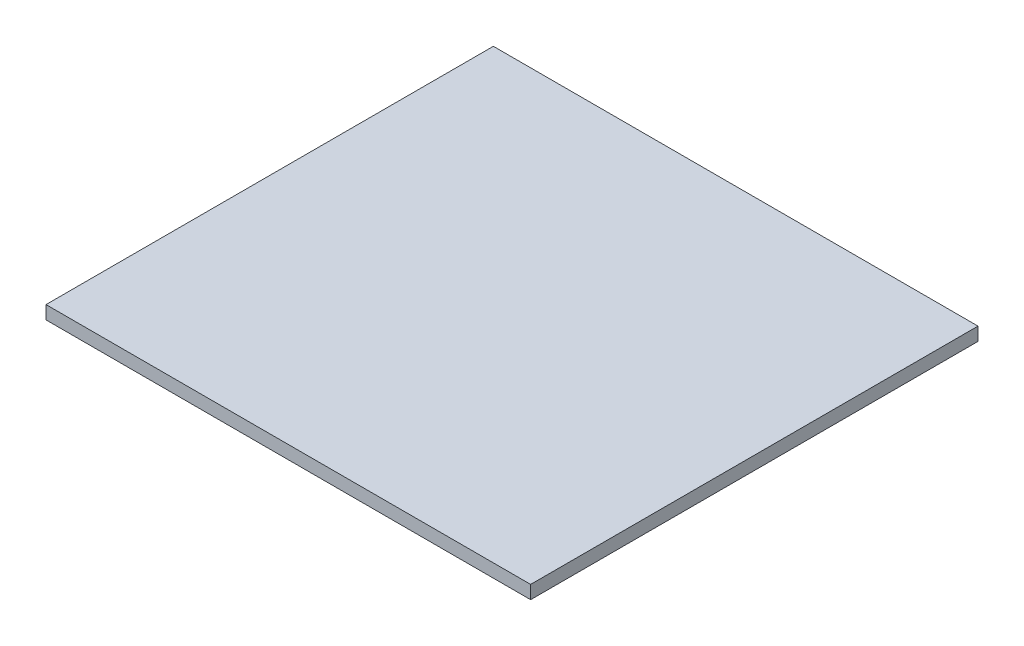
SolidWorks part; units mm, degrees
ref_plane "Front Plane" through (0, 0, 0) normal (0, 0, 1) x (1, 0, 0)
ref_plane "Top Plane" through (0, 0, 0) normal (0, 1, 0) x (1, 0, 0)
ref_plane "Right Plane" through (0, 0, 0) normal (1, 0, 0) x (0, 0, -1)
sketch "Sketch2" plane through (0, 0, 0) normal (0, 1, 0) x (1, 0, 0)
  line L1 (-118.587, 65.1335) -> (-36.037, 65.1335)
  line L2 (-118.587, 65.1335) -> (-118.587, -11.0665)
  line L3 (-118.587, -11.0665) -> (-36.037, -11.0665)
  line L4 (-36.037, 65.1335) -> (-36.037, -11.0665)
  dimension "D1" = 82.55
  dimension "D2" = 76.2
extrude "Boss-Extrude1" add sketch "Sketch2" along normal blind 2.2606
